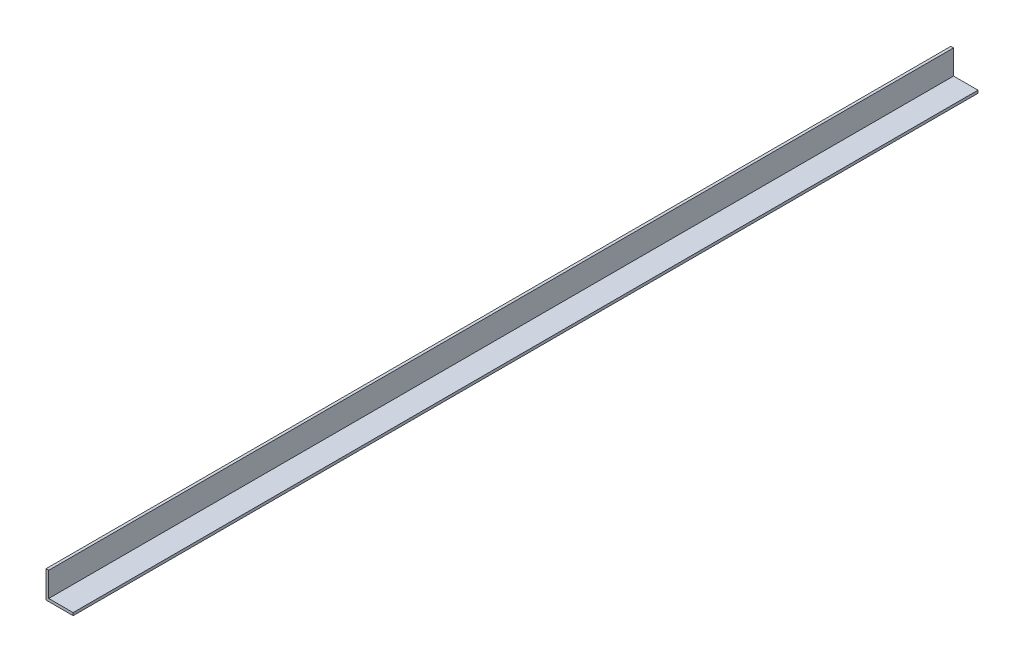
SolidWorks part; units mm, degrees
material "6063 T5"
ref_plane "Спереди" through (0, 0, 0) normal (0, 0, 1) x (1, 0, 0)
ref_plane "Сверху" through (0, 0, 0) normal (0, 1, 0) x (1, 0, 0)
ref_plane "Справа" through (0, 0, 0) normal (1, 0, 0) x (0, 0, -1)
sketch "Эскиз1" plane through (0, 0, 0) normal (0, 0, 1) x (1, 0, 0)
  line L0 (0, 30) -> (0, 0)
  line L1 (0, 0) -> (30, 0)
  line L2 (30, 0) -> (30, 3)
  line L3 (30, 3) -> (3, 3)
  line L4 (3, 3) -> (3, 30)
  line L5 (3, 30) -> (0, 30)
  dimension "D1" = 30
  dimension "D2" = 3
extrude "Бобышка-Вытянуть1" add sketch "Эскиз1" along normal blind 1000
